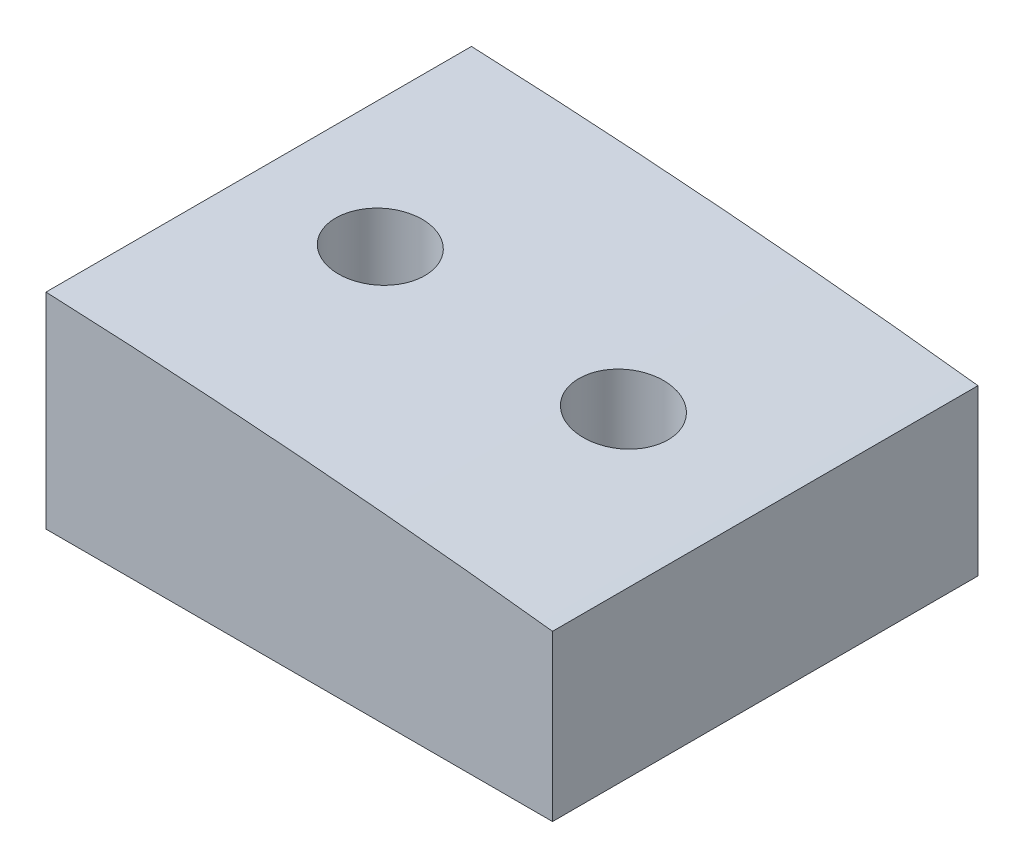
SolidWorks part; units mm, degrees
material "Alu 2017 (AU4G)"
ref_plane "Face" through (0, 0, 0) normal (0, 0, 1) x (1, 0, 0)
ref_plane "Dessus" through (0, 0, 0) normal (0, 1, 0) x (1, 0, 0)
ref_plane "Droite" through (0, 0, 0) normal (1, 0, 0) x (0, 0, -1)
sketch "Esquisse1" plane through (0, 0, 0) normal (0, 0, 1) x (1, 0, 0)
  line L0 (0, 0) -> (37.5, 0)
  line L1 (37.5, 0) -> (37.5, 12.2)
  line L2 (0, 0) -> (0, 15.2)
  arc A0 (0, 15.2) -> (37.5, 12.2) centre (-21.0944, -484.3548) cw
  dimension "D4" = 500
  dimension "D1" = 12.2
  dimension "D2" = 15.2
  dimension "D3" = 37.5
extrude "Boss.-Extru.1" add sketch "Esquisse1" along normal mid plane 31.5
hole_wizard "Dégagement M61" positions "Esquisse3" profile "Esquisse2" hole size "M6" standard "ISO" end condition through all
sketch "Esquisse3" plane through (0, 0, 0) normal (0, -1, 0) x (-1, 0, 0)
  point P0 (-9, 0)
  point P2 (-27, 0)
  dimension "D1" = 9
  dimension "D2" = 18
sketch "Esquisse2" plane through (9, 0, 0) normal (1, 0, 0) x (0, 0, -1)
  line L0 (0, 0) -> (0, 15.2)
  line L1 (0, 15.2) -> (3.3, 15.2)
  line L2 (3.3, 15.2) -> (3.3, 0)
  line L5 (3.3, 0) -> (0, 0)
  line L11 (0, -6.35) -> (0, 107.95) construction
  dimension "Diamètre du perçage jusqu'au prochain" = 6.6
  dimension "Profondeur du perçage jusqu'au prochain" = 15.2
